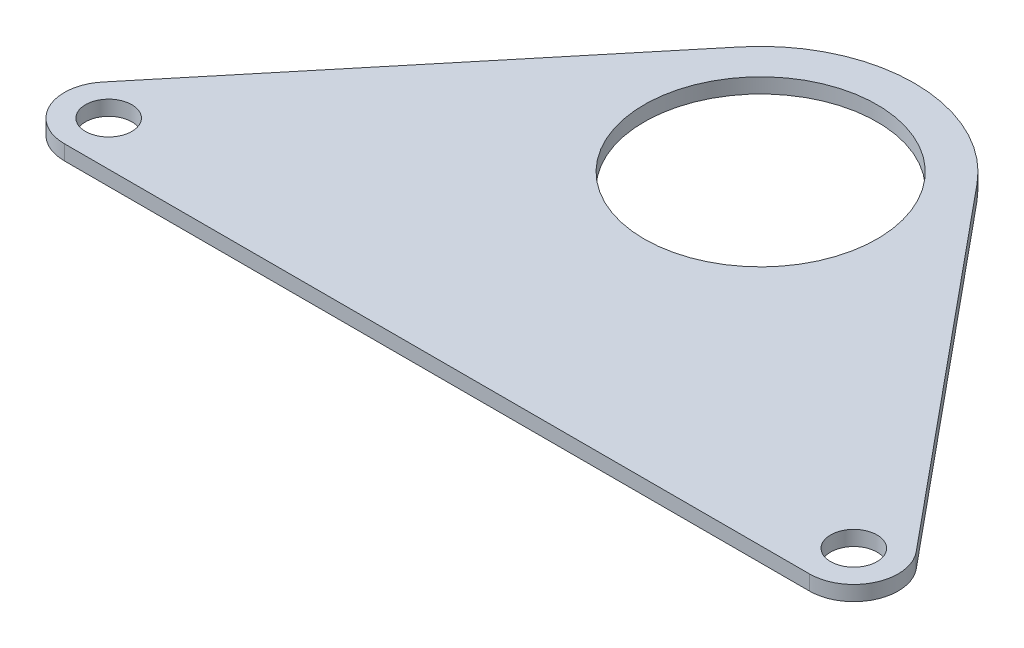
SolidWorks part; units mm, degrees
material "6061-T6 (SS)"
ref_plane "Front Plane" through (0, 0, 0) normal (0, 0, 1) x (1, 0, 0)
ref_plane "Top Plane" through (0, 0, 0) normal (0, 1, 0) x (1, 0, 0)
ref_plane "Right Plane" through (0, 0, 0) normal (1, 0, 0) x (0, 0, -1)
sketch "Sketch1" plane through (0, 0, 0) normal (0, 1, 0) x (1, 0, 0)
  line L0 (-60.5982, -30) -> (77.5967, -30) construction
  line L1 (46.1768, -30) -> (46.5785, -30.4865)
  line L2 (-12.7221, 10.5071) -> (-43.672, -26.9673)
  line L3 (-40, -34.7625) -> (40, -34.7625)
  line L4 (12.7221, 10.5071) -> (43.672, -26.9673)
  line L5 (0, 0) -> (0, -9.1082) construction
  circle A0 centre (0, 0) radius 12.5
  arc A1 (12.7221, 10.5071) -> (-12.7221, 10.5071) centre (0, 0) ccw
  arc A2 (40, -34.7625) -> (43.672, -26.9673) centre (40, -30) ccw
  arc A3 (-40, -34.7625) -> (-43.672, -26.9673) centre (-40, -30) cw
  point P8 (0, -34.7625)
  dimension "D1" = 25
  dimension "D2" = 33
  dimension "D5" = 9.525
  dimension "D3" = 30
  dimension "D4" = 40
extrude "Boss-Extrude1" add sketch "Sketch1" along normal blind 1.6002 contours A3 L3 A2 L4 A1 L2 A0
hole_wizard "#10 Clearance Hole1" positions "Sketch3" profile "Sketch2" hole size "#10" standard "ANSI Inch"
sketch "Sketch3" plane through (0, 1.6002, 0) normal (0, 1, 0) x (1, 0, 0)
  line L0 (0, 0) -> (0, -6.8264) construction
  arc A0 (40, -34.7625) -> (43.672, -26.9673) centre (40, -30) ccw construction
  point P0 (40, -30)
  point P10 (-40, -30)
sketch "Sketch2" plane through (40, 1.6002, 30) normal (1, 0, 0) x (0, 0, 1)
  line L0 (0, 0) -> (0, 174.4657)
  line L1 (0, 174.4657) -> (2.4892, 172.97)
  line L2 (2.4892, 172.97) -> (2.4892, 0)
  line L5 (2.4892, 0) -> (0, 0)
  line L10 (0, 174.4657) -> (-2.4892, 172.97) construction
  line L11 (0, -6.35) -> (0, 107.95) construction
  dimension "Hole Dia." = 4.9784
  dimension "Hole Depth" = 172.97
  dimension "Drill Angle" = 118
